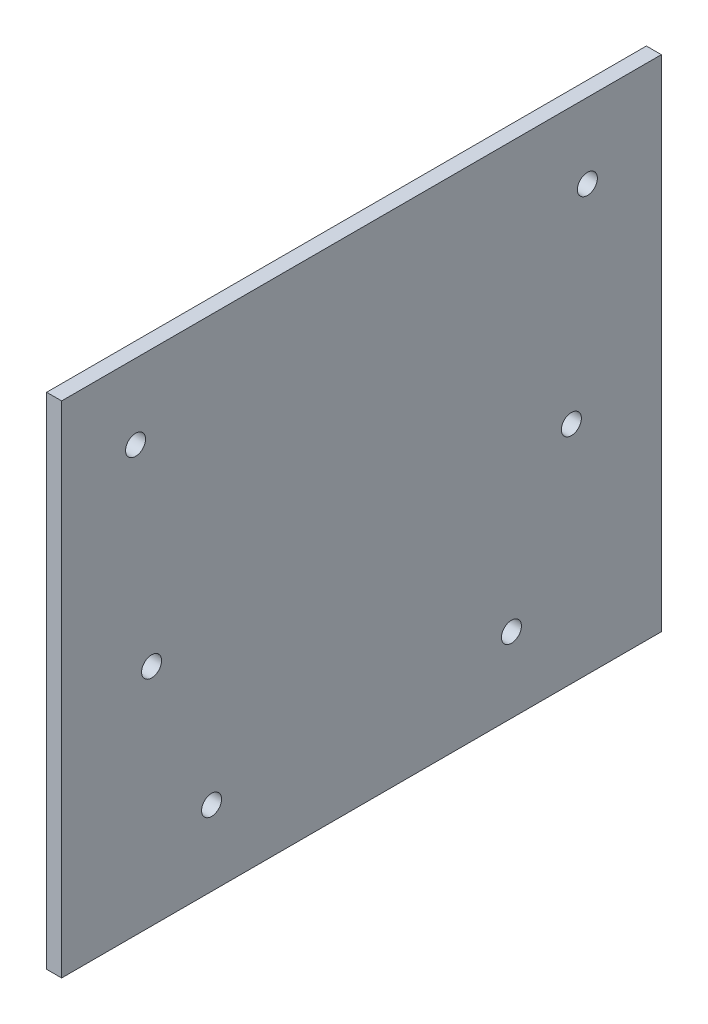
SolidWorks part; units mm, degrees
ref_plane "Front Plane" through (0, 0, 0) normal (0, 0, 1) x (1, 0, 0)
ref_plane "Top Plane" through (0, 0, 0) normal (0, 1, 0) x (1, 0, 0)
ref_plane "Right Plane" through (0, 0, 0) normal (1, 0, 0) x (0, 0, -1)
sketch "Sketch1" plane through (0, 0, 0) normal (1, 0, 0) x (0, 0, -1)
  line L1 (-33.8535, 49.9811) -> (86.1465, 49.9811)
  line L2 (-33.8535, 49.9811) -> (-33.8535, -50.0189)
  line L3 (-33.8535, -50.0189) -> (86.1465, -50.0189)
  line L4 (86.1465, 49.9811) -> (86.1465, -50.0189)
  dimension "D1" = 120
  dimension "D2" = 100
extrude "Boss-Extrude1" add sketch "Sketch1" along normal blind 3
sketch "Sketch2" plane through (3, 0, 0) normal (1, 0, 0) x (0, 0, -1)
  circle A0 centre (-3.8535, -35.0189) radius 2
  circle A1 centre (56.1465, -35.0189) radius 2
  dimension "D1" = 4
  dimension "D2" = 4
extrude "Cut-Extrude1" cut sketch "Sketch2" against normal through all
sketch "Sketch3" plane through (0, 0, 0) normal (-1, 0, 0) x (0, 0, 1)
  circle A0 centre (-68.1465, -5.0189) radius 2
  circle A1 centre (15.8535, -5.0189) radius 2
  dimension "D1" = 4
extrude "Cut-Extrude2" cut sketch "Sketch3" against normal through all
sketch "Sketch4" plane through (0, 0, 0) normal (-1, 0, 0) x (0, 0, 1)
  circle A0 centre (19.0556, 34.9811) radius 2
  circle A1 centre (-71.3485, 34.9811) radius 2
  dimension "D1" = 4
  dimension "D2" = 4
extrude "Cut-Extrude3" cut sketch "Sketch4" against normal through all
